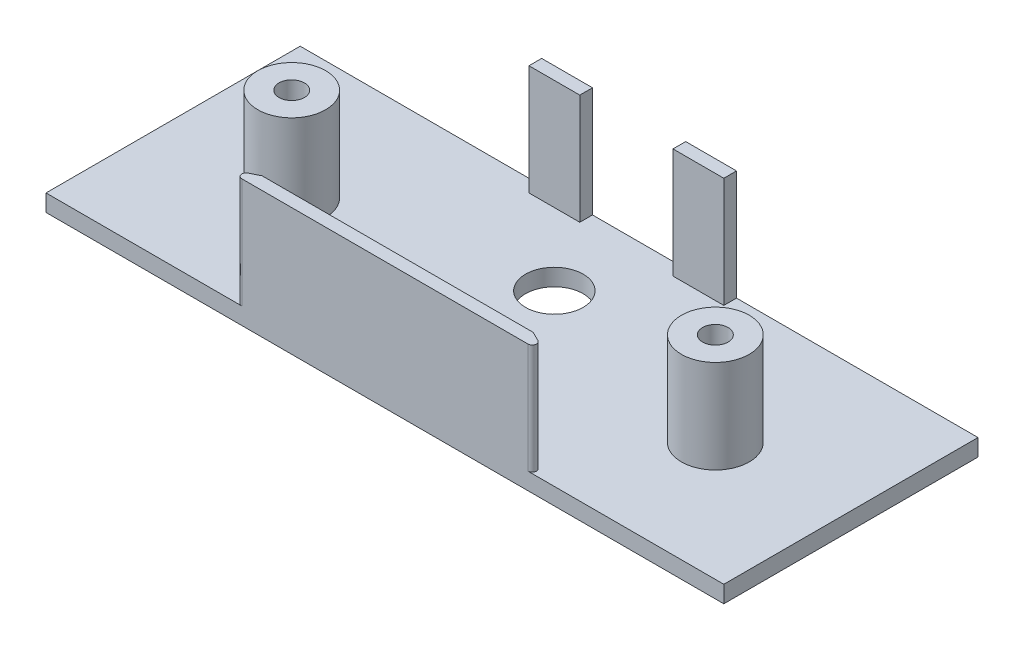
SolidWorks part; units mm, degrees
ref_plane "Front Plane" through (0, 0, 0) normal (0, 0, 1) x (1, 0, 0)
ref_plane "Top Plane" through (0, 0, 0) normal (0, 1, 0) x (1, 0, 0)
ref_plane "Right Plane" through (0, 0, 0) normal (1, 0, 0) x (0, 0, -1)
sketch "Sketch1" plane through (0, 0, 0) normal (0, 1, 0) x (1, 0, 0)
  line L0 (0, 0) -> (50, 0) construction
  line L1 (0, 14) -> (50, 14) construction
  line L2 (0, -14) -> (50, -14) construction
  line L3 (0, 14) -> (25, 6) construction
  line L4 (25, 6) -> (50, 14) construction
  line L5 (25, 6) -> (25, 14) construction
  line L6 (28.6587, 1.2446) -> (41.463, 11.096)
  line L7 (21.3413, 1.2446) -> (8.537, 11.096)
  circle A0 centre (0, 0) radius 14 construction
  circle A1 centre (50, 0) radius 14 construction
  circle A2 centre (25, 6) radius 6 construction
  arc A3 (8.537, 11.096) -> (0, -14) centre (0, 0) ccw
  arc A4 (41.463, 11.096) -> (50, -14) centre (50, 0) cw
  arc A5 (21.3413, 1.2446) -> (28.6587, 1.2446) centre (25, 6) ccw
  dimension "D1" = 28
  dimension "D2" = 12
  dimension "D3" = 50
  dimension "D4" = 8
sketch "Sketch2" plane through (0, 0, 0) normal (0, 1, 0) x (1, 0, 0)
  line L0 (65, -14) -> (65, 16)
  line L1 (-15, 16) -> (65, 16)
  line L3 (-15, -14) -> (65, -14)
  line L5 (0, -14) -> (50, -14) construction
  line L9 (0, 14) -> (50, 14) construction
  line L10 (-15, -14) -> (-15, 16)
  line L11 (25, -14) -> (25, 0) construction
  line L13 (0, 0) -> (50, 0) construction
  circle A4 centre (0, 0) radius 1.5
  circle A5 centre (50, 0) radius 1.5
  circle A6 centre (25, 6) radius 3.4
extrude "Boss-Extrude1" add sketch "Sketch2" along normal blind 2
sketch "Sketch3" plane through (0, 2, 0) normal (0, 1, 0) x (1, 0, 0)
  line L0 (0, -14) -> (50, -14) construction
  line L1 (6, -14) -> (44, -14)
  line L2 (6, -14) -> (9, -12.5)
  line L3 (9, -12.5) -> (41, -12.5)
  line L4 (44, -14) -> (41, -12.5)
  line L6 (13.5, 16) -> (19.5, 16)
  line L7 (13.5, 16) -> (13.5, 14.5)
  line L8 (13.5, 14.5) -> (19.5, 14.5)
  line L9 (19.5, 16) -> (19.5, 14.5)
  line L10 (16.5, 16) -> (25, 16) construction
  line L11 (30.5, 16) -> (36.5, 16)
  line L12 (30.5, 16) -> (30.5, 14.5)
  line L13 (30.5, 14.5) -> (36.5, 14.5)
  line L14 (36.5, 16) -> (36.5, 14.5)
  line L15 (25, 16) -> (33.5, 16) construction
  line L16 (25, -12.5) -> (25, -14) construction
  line L17 (65, 16) -> (-15, 16) construction
extrude "Boss-Extrude2" add sketch "Sketch3" along normal blind 13
sketch "Sketch9" plane through (0, 2, 0) normal (0, 1, 0) x (1, 0, 0)
  circle A2 centre (50, 0) radius 1.5
  circle A3 centre (50, 0) radius 1.5
  circle A4 centre (50, 0) radius 4
  circle A5 centre (0, 0) radius 1.5
  circle A6 centre (0, 0) radius 1.5
  circle A7 centre (0, 0) radius 4
extrude "Boss-Extrude4" add sketch "Sketch9" along normal blind 11
fillet "Fillet1" radius 0.5 2 edges at (6, 8.5, 14) (44, 8.5, 14)
chamfer "Chamfer1" distance 2 angle 45 1 edges at (25, 2, 12.5)
equation "\"D4@Sketch2\"=\"D3@Sketch2\""
equation "\"D8@Sketch3\"=\"D5@Sketch3\""
equation "\"D4@Sketch9\"=\"D3@Sketch9\""
